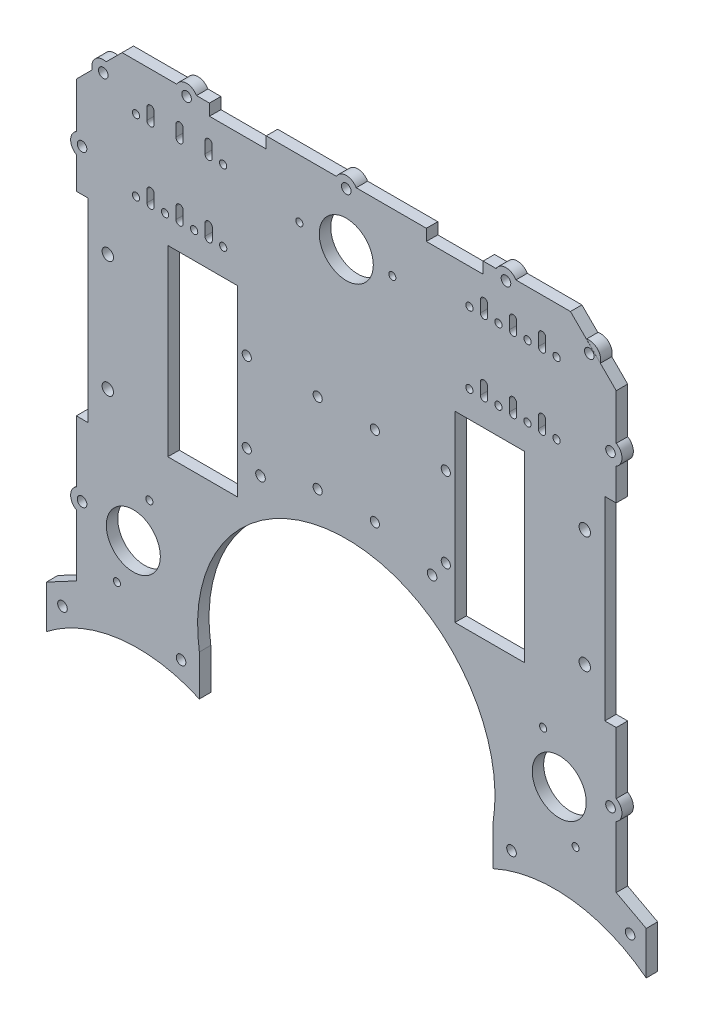
SolidWorks part; units mm, degrees
ref_plane "Front Plane" through (0, 0, 0) normal (0, 0, 1) x (1, 0, 0)
ref_plane "Top Plane" through (0, 0, 0) normal (0, 1, 0) x (1, 0, 0)
ref_plane "Right Plane" through (0, 0, 0) normal (1, 0, 0) x (0, 0, -1)
sketch "Sketch1" plane through (0, 0, 0) normal (0, 0, 1) x (1, 0, 0)
  line L0 (64.2262, -107) -> (118, -107)
  line L1 (-98, 103) -> (98, 103)
  line L3 (-118, -107) -> (-64.2262, -107)
  line L5 (-150, 100) -> (150, -100) construction
  line L6 (-150, -100) -> (150, 100) construction
  line L10 (0, 0) -> (0, 48.5738) construction
  line L12 (-47.5, 0) -> (47.5, 0) construction
  line L13 (47.5, -40) -> (47.5, 40)
  line L14 (47.5, 40) -> (78, 40)
  line L15 (78, 40) -> (78, -40)
  line L16 (78, -40) -> (47.5, -40)
  line L17 (-78, -40) -> (-47.5, -40)
  line L18 (-47.5, -40) -> (-47.5, 40)
  line L19 (-78, 40) -> (-78, -40)
  line L20 (-47.5, 40) -> (-78, 40)
  line L21 (78, 0) -> (118, 0) construction
  line L22 (118, 83) -> (118, -107)
  line L23 (-118, 83) -> (-118, -107)
  line L24 (-98, 103) -> (-98, 83) construction
  line L25 (-98, 83) -> (-118, 83) construction
  line L26 (0, 103) -> (0, -97) construction
  line L27 (-118, 83) -> (-98, 103)
  line L28 (98, 103) -> (118, 83)
  arc A0 (64.2262, -107) -> (-64.2262, -107) centre (0, -97) ccw
  point P0 (0, 0)
  point P19 (0, 0)
  point P22 (47.5, 0)
  point P33 (118, 0)
  dimension "D2" = 130
  dimension "D1" = 210
  dimension "D3" = 63
  dimension "D4" = 20
  dimension "D5" = 20
  dimension "D6" = 95
  dimension "D7" = 80
  dimension "D8" = 30.5
  dimension "D9" = 40
extrude "Boss-Extrude1" add sketch "Sketch1" along normal blind 5
sketch "Sketch2" plane through (0, 0, 5) normal (0, 0, 1) x (1, 0, 0)
  circle A0 centre (43.5, 15.5) radius 2
  circle A1 centre (43.5, -19.5) radius 2
  circle A2 centre (12.5, -19.5) radius 2
  circle A3 centre (12.5, 15.5) radius 2
  circle A4 centre (-12.5, 15.5) radius 2
  circle A5 centre (-12.5, -19.5) radius 2
  circle A6 centre (-43.5, -19.5) radius 2
  circle A7 centre (-43.5, 15.5) radius 2
extrude "Cut-Extrude1" cut sketch "Sketch2" against normal through all
sketch "Sketch3" plane through (0, 0, 5) normal (0, 0, 1) x (1, 0, 0)
  line L0 (-85.5875, 82.747) -> (-85.5875, 87.747) construction
  line L1 (-85.5875, 85.247) -> (-88.4029, 85.247) construction
  line L2 (-84, 87.747) -> (-84, 82.747)
  line L3 (-87.175, 87.747) -> (-87.175, 82.747)
  line L4 (-72.8875, 82.747) -> (-72.8875, 87.747) construction
  line L5 (-60.1875, 82.747) -> (-60.1875, 87.747) construction
  line L6 (-74.4775, 87.747) -> (-74.475, 82.747)
  line L7 (-71.2975, 87.747) -> (-71.3, 82.747)
  line L8 (-61.7775, 87.747) -> (-61.775, 82.747)
  line L9 (-58.5975, 87.747) -> (-58.6, 82.747)
  line L10 (-83.9734, 56.5828) -> (-83.9734, 51.5828)
  line L11 (-87.1484, 56.5828) -> (-87.1484, 51.5828)
  line L12 (-74.4509, 56.5828) -> (-74.4484, 51.5828)
  line L13 (-71.2709, 56.5828) -> (-71.2734, 51.5828)
  line L14 (-61.7509, 56.5828) -> (-61.7484, 51.5828)
  line L15 (-58.5709, 56.5828) -> (-58.5734, 51.5828)
  line L16 (0, 103) -> (0, 110.8506) construction
  line L17 (98, 103) -> (-98, 103) construction
  line L18 (60.1875, 82.747) -> (60.1875, 87.747) construction
  line L19 (72.8875, 82.747) -> (72.8875, 87.747) construction
  line L20 (85.5875, 85.247) -> (88.4029, 85.247) construction
  line L21 (85.5875, 82.747) -> (85.5875, 87.747) construction
  line L22 (58.5709, 56.5828) -> (58.5734, 51.5828)
  line L23 (61.7509, 56.5828) -> (61.7484, 51.5828)
  line L24 (71.2709, 56.5828) -> (71.2734, 51.5828)
  line L25 (74.4509, 56.5828) -> (74.4484, 51.5828)
  line L26 (87.1484, 56.5828) -> (87.1484, 51.5828)
  line L27 (83.9734, 56.5828) -> (83.9734, 51.5828)
  line L28 (58.5975, 87.747) -> (58.6, 82.747)
  line L29 (61.7775, 87.747) -> (61.775, 82.747)
  line L30 (71.2975, 87.747) -> (71.3, 82.747)
  line L31 (74.4775, 87.747) -> (74.475, 82.747)
  line L32 (87.175, 87.747) -> (87.175, 82.747)
  line L33 (84, 87.747) -> (84, 82.747)
  circle A0 centre (20.1383, 77.5) radius 1.55
  circle A1 centre (-20.5035, 77.5) radius 1.55
  circle A2 centre (-53.8375, 82.747) radius 1.5875
  circle A3 centre (-66.5375, 82.747) radius 1.5875
  circle A4 centre (-79.2375, 82.747) radius 1.5875
  circle A5 centre (-91.9375, 82.747) radius 1.5875
  circle A6 centre (0, 77.5) radius 11.8076
  circle A11 centre (-104.25, 23.5) radius 2.5
  circle A12 centre (-104.25, -27.5) radius 2.5
  circle A13 centre (104.25, 23.5) radius 2.5
  circle A14 centre (104.25, -27.5) radius 2.5
  circle A15 centre (86.0568, -60.5122) radius 1.55
  circle A16 centre (100.255, -98.5932) radius 1.55
  circle A17 centre (-86.0568, -60.5122) radius 1.55
  circle A18 centre (-100.255, -98.5932) radius 1.55
  arc A19 (-87.175, 82.747) -> (-84, 82.747) centre (-85.5875, 82.747) ccw
  arc A20 (-87.175, 87.747) -> (-84, 87.747) centre (-85.5875, 87.747) cw
  arc A21 (-74.475, 82.747) -> (-71.3, 82.747) centre (-72.8875, 82.747) ccw
  arc A22 (-61.775, 82.747) -> (-58.6, 82.747) centre (-60.1875, 82.747) ccw
  arc A23 (-71.2975, 87.747) -> (-74.4775, 87.747) centre (-72.8875, 87.747) ccw
  arc A24 (-58.5975, 87.747) -> (-61.7775, 87.747) centre (-60.1875, 87.747) ccw
  arc A25 (-61.775, 82.747) -> (-58.6, 82.747) centre (-60.1875, 82.747) ccw
  arc A27 (-87.1484, 56.5828) -> (-83.9734, 56.5828) centre (-85.5609, 56.5828) cw
  arc A28 (-87.1484, 51.5828) -> (-83.9734, 51.5828) centre (-85.5609, 51.5828) ccw
  arc A29 (-71.2709, 56.5828) -> (-74.4509, 56.5828) centre (-72.8609, 56.5828) ccw
  arc A30 (-74.4484, 51.5828) -> (-71.2734, 51.5828) centre (-72.8609, 51.5828) ccw
  arc A31 (-58.5709, 56.5828) -> (-61.7509, 56.5828) centre (-60.1609, 56.5828) ccw
  arc A32 (-61.7484, 51.5828) -> (-58.5734, 51.5828) centre (-60.1609, 51.5828) ccw
  circle A33 centre (-91.9109, 51.5828) radius 1.5875
  circle A34 centre (-79.2109, 51.5828) radius 1.5875
  circle A35 centre (-66.5109, 51.5828) radius 1.5875
  circle A36 centre (-53.8109, 51.5828) radius 1.5875
  circle A37 centre (53.8109, 51.5828) radius 1.5875
  circle A38 centre (66.5109, 51.5828) radius 1.5875
  circle A39 centre (79.2109, 51.5828) radius 1.5875
  circle A40 centre (91.9109, 51.5828) radius 1.5875
  arc A41 (61.7484, 51.5828) -> (58.5734, 51.5828) centre (60.1609, 51.5828) cw
  arc A42 (58.5709, 56.5828) -> (61.7509, 56.5828) centre (60.1609, 56.5828) cw
  arc A43 (74.4484, 51.5828) -> (71.2734, 51.5828) centre (72.8609, 51.5828) cw
  arc A44 (71.2709, 56.5828) -> (74.4509, 56.5828) centre (72.8609, 56.5828) cw
  arc A45 (87.1484, 51.5828) -> (83.9734, 51.5828) centre (85.5609, 51.5828) cw
  arc A46 (87.1484, 56.5828) -> (83.9734, 56.5828) centre (85.5609, 56.5828) ccw
  arc A47 (61.775, 82.747) -> (58.6, 82.747) centre (60.1875, 82.747) cw
  arc A48 (58.5975, 87.747) -> (61.7775, 87.747) centre (60.1875, 87.747) cw
  arc A49 (71.2975, 87.747) -> (74.4775, 87.747) centre (72.8875, 87.747) cw
  arc A50 (61.775, 82.747) -> (58.6, 82.747) centre (60.1875, 82.747) cw
  arc A51 (74.475, 82.747) -> (71.3, 82.747) centre (72.8875, 82.747) cw
  arc A52 (87.175, 87.747) -> (84, 87.747) centre (85.5875, 87.747) ccw
  arc A53 (87.175, 82.747) -> (84, 82.747) centre (85.5875, 82.747) cw
  circle A54 centre (91.9375, 82.747) radius 1.5875
  circle A55 centre (79.2375, 82.747) radius 1.5875
  circle A56 centre (66.5375, 82.747) radius 1.5875
  circle A57 centre (53.8375, 82.747) radius 1.5875
  circle A58 centre (93.0921, -79.3816) radius 11.8076
  circle A59 centre (-93.0921, -79.3816) radius 11.8076
  dimension "D4" = 3.18
  dimension "D1" = 5
  dimension "D3" = 5
  dimension "D5" = 2
  dimension "D6" = 2
extrude "Cut-Extrude2" cut sketch "Sketch3" against normal through all contours A6 | A0 | A1 | L7 A23 L6 A21 | L9 A24 L8 A22 | A20 L3 A19 L2 | A5 | A33 | L11 A28 L10 A27 | L12 A30 L13 A29 | A34 | L14 A32 L15 A31 | A35 | A36 | A53 L32 A52 L33 | A55 | A51 L31 A49 L30 | A48 L28 A47 L29 | A57 | A56 | A54 | L26 A46 L27 A45 | A40 | A39 | A44 L24 A43 L25 | A38 | A42 L22 A41 L23 | A37 | A13 | A14 | A58 | A15 | A16 | A11 | A12 | A59 | A18 | A17 | A2
sketch "Sketch4" plane through (0, 0, 5) normal (0, 0, 1) x (1, 0, 0)
  line L0 (-118, -2) -> (-113, -2) construction
  line L1 (-118, 83) -> (-118, -107) construction
  line L2 (-113, 40.5) -> (-113, -44.5)
  line L3 (-113, 40.5) -> (-118, 40.5)
  line L4 (-118, 40.5) -> (-118, -44.5)
  line L5 (-118, -44.5) -> (-113, -44.5)
  line L6 (0, 103) -> (0, 94.0884) construction
  line L7 (98, 103) -> (-98, 103) construction
  line L8 (118, -2) -> (113, -2) construction
  line L9 (118, -44.5) -> (113, -44.5)
  line L10 (118, 40.5) -> (118, -44.5)
  line L11 (113, 40.5) -> (118, 40.5)
  line L12 (113, 40.5) -> (113, -44.5)
  point P7 (-113, -2)
  point P20 (113, -2)
  dimension "D1" = 5
  dimension "D2" = 85
extrude "Cut-Extrude3" cut sketch "Sketch4" against normal through all
sketch "Sketch7" plane through (0, 0, 0) normal (0, 0, -1) x (-1, 0, 0)
  line L0 (-98, 103) -> (98, 103) construction
  line L1 (-59.8, 98) -> (-35, 98)
  line L2 (-59.8, 98) -> (-59.8, 103)
  line L3 (-59.8, 103) -> (-35, 103)
  line L4 (-35, 98) -> (-35, 103)
  line L5 (-59.8, 98) -> (-35, 103) construction
  line L6 (-59.8, 103) -> (-35, 98) construction
  line L7 (-35, 98) -> (-35, 103) construction
  line L8 (59.8, 98) -> (59.8, 103) construction
  line L9 (35, 98) -> (59.8, 98)
  line L10 (35, 98) -> (35, 103)
  line L11 (35, 103) -> (59.8, 103)
  line L12 (59.8, 98) -> (59.8, 103)
  line L13 (35, 98) -> (59.8, 103) construction
  line L14 (35, 103) -> (59.8, 98) construction
  line L15 (-35, 100.5) -> (35, 100.5) construction
  line L16 (59.8, 100.5) -> (69.8, 100.5) construction
  line L17 (-59.8, 100.5) -> (-69.8, 100.5) construction
  circle A0 centre (0, 100.5) radius 2.1
  circle A1 centre (69.8, 100.5) radius 2.1
  circle A2 centre (-69.8, 100.5) radius 2.1
  point P4 (-47.4, 100.5)
  point P14 (47.4, 100.5)
  dimension "D3" = 4.2
  dimension "D1" = 10
  dimension "D2" = 10
extrude "Cut-Extrude5" cut sketch "Sketch7" against normal through all
sketch "Sketch8" plane through (0, 0, 0) normal (0, 0, -1) x (-1, 0, 0)
  line L0 (-74.1301, 103) -> (-65.4699, 103)
  line L1 (-98, 103) -> (-59.8, 103) construction
  line L2 (-4.3301, 103) -> (4.3301, 103)
  line L3 (-35, 103) -> (35, 103) construction
  line L4 (65.4699, 103) -> (74.1301, 103)
  line L5 (59.8, 103) -> (98, 103) construction
  arc A0 (74.1301, 103) -> (65.4699, 103) centre (69.8, 100.5) ccw
  arc A1 (4.3301, 103) -> (-4.3301, 103) centre (0, 100.5) ccw
  arc A2 (-65.4699, 103) -> (-74.1301, 103) centre (-69.8, 100.5) ccw
  dimension "D1" = 10
extrude "Boss-Extrude3" add sketch "Sketch8" against normal up to surface (5 mm away) up to face at (0, 33.625, 5)
sketch "Sketch9" plane through (0, 0, 5) normal (0, 0, 1) x (1, 0, 0)
  circle A0 centre (37.5, -27) radius 2.1
  circle A1 centre (-37.5, -27) radius 2.1
extrude "Cut-Extrude6" cut sketch "Sketch9" against normal through all
sketch "Sketch10" plane through (0, 0, 0) normal (0, 0, -1) x (-1, 0, 0)
  line L0 (-118, -75.75) -> (-113, -75.75) construction
  line L1 (-118, -107) -> (-118, -44.5) construction
  line L2 (0, 0) -> (0, -17.3578) construction
  line L3 (113, 58.75) -> (118, 58.75) construction
  line L4 (113, 60.85) -> (113, 56.65) construction
  line L5 (118, 83) -> (118, 40.5) construction
  line L6 (-113, 58.75) -> (-118, 58.75) construction
  line L7 (-113, 56.65) -> (-113, 60.85) construction
  line L8 (-118, 40.5) -> (-118, 83) construction
  line L9 (-108, 93) -> (-104.466, 89.463) construction
  line L10 (-118, 83) -> (-98, 103) construction
  circle A0 centre (-115.5, -75.75) radius 2.1
  circle A1 centre (115.5, -75.75) radius 2.1
  circle A2 centre (-115.5, 58.75) radius 2.1
  circle A3 centre (115.5, 58.75) radius 2.1
  circle A4 centre (-106.233, 91.2315) radius 2.1
  circle A5 centre (106.233, 91.2315) radius 2.1
  dimension "D2" = 4.2
  dimension "D3" = 4.2
  dimension "D4" = 4.2
  dimension "D5" = 4.2
  dimension "D1" = 5
extrude "Cut-Extrude7" cut sketch "Sketch10" against normal blind 5
sketch "Sketch11" plane through (0, 0, 0) normal (0, 0, -1) x (-1, 0, 0)
  line L0 (-118, 54.4199) -> (-118, 63.0801)
  line L1 (-118, 40.5) -> (-118, 83) construction
  line L2 (-118, -71.4199) -> (-118, -80.0801)
  line L3 (-118, -107) -> (-118, -44.5) construction
  line L4 (118, -71.4199) -> (118, -80.0801)
  line L5 (118, -44.5) -> (118, -107) construction
  line L6 (118, 63.0801) -> (118, 54.4199)
  line L7 (118, 83) -> (118, 40.5) construction
  line L8 (104.9389, 96.0611) -> (111.0626, 89.9374)
  line L9 (98, 103) -> (118, 83) construction
  line L10 (-104.9992, 96.0769) -> (-111.0626, 89.9374)
  line L11 (-118, 83) -> (-98, 103) construction
  arc A0 (-118, 63.0801) -> (-118, 54.4199) centre (-115.5, 58.75) ccw
  arc A1 (-118, -71.4199) -> (-118, -80.0801) centre (-115.5, -75.75) ccw
  arc A2 (118, -80.0801) -> (118, -71.4199) centre (115.5, -75.75) ccw
  arc A3 (118, 54.4199) -> (118, 63.0801) centre (115.5, 58.75) ccw
  arc A4 (-104.9992, 96.0769) -> (-111.0626, 89.9374) centre (-106.233, 91.2315) ccw
  arc A5 (111.0626, 89.9374) -> (104.9389, 96.0611) centre (106.233, 91.2315) ccw
  dimension "D1" = 10
extrude "Boss-Extrude4" add sketch "Sketch11" against normal blind 5
sketch "Sketch12" plane through (0, 0, 0) normal (0, 0, -1) x (-1, 0, 0)
  line L0 (-91.1131, -107) -> (-91.1131, -114) construction
  line L1 (-64.2262, -107) -> (-118, -107) construction
  line L2 (-91.1131, -114) -> (-131.1131, -114) construction
  line L3 (-118, -107) -> (-131.1131, -114)
  line L5 (-91.1131, -114) -> (-91.1131, -184) construction
  line L6 (-131.1131, -114) -> (-131.1131, -132.7652)
  line L8 (-118, -107) -> (-64.2262, -107)
  line L9 (0, -107) -> (0, -144.2151) construction
  line L10 (118, -107) -> (-118, -107) construction
  line L11 (91.1131, -114) -> (131.1131, -114) construction
  line L12 (91.1131, -107) -> (91.1131, -114) construction
  line L13 (118, -107) -> (64.2262, -107)
  line L15 (131.1131, -114) -> (131.1131, -132.7652)
  line L17 (118, -107) -> (131.1131, -114)
  line L18 (-64.2262, -107) -> (-64.2262, -124.8215)
  line L19 (64.2262, -107) -> (64.2262, -124.8215)
  arc A1 (-64.2262, -124.8215) -> (-131.1131, -132.7652) centre (-91.1131, -184) ccw
  arc A2 (64.2262, -124.8215) -> (131.1131, -132.7652) centre (91.1131, -184) cw
  dimension "D4" = 130
  dimension "D1" = 7
  dimension "D2" = 40
  dimension "D3" = 70
extrude "Boss-Extrude5" add sketch "Sketch12" against normal blind 5
sketch "Sketch13" plane through (0, 0, 0) normal (0, 0, -1) x (-1, 0, 0)
  circle A0 centre (-72.2281, -114) radius 2.1
  circle A1 centre (-124.0554, -119.6157) radius 2.1
  circle A2 centre (124.0554, -119.6157) radius 2.1
  circle A3 centre (72.2281, -114) radius 2.1
extrude "Cut-Extrude8" cut sketch "Sketch13" against normal blind 10
